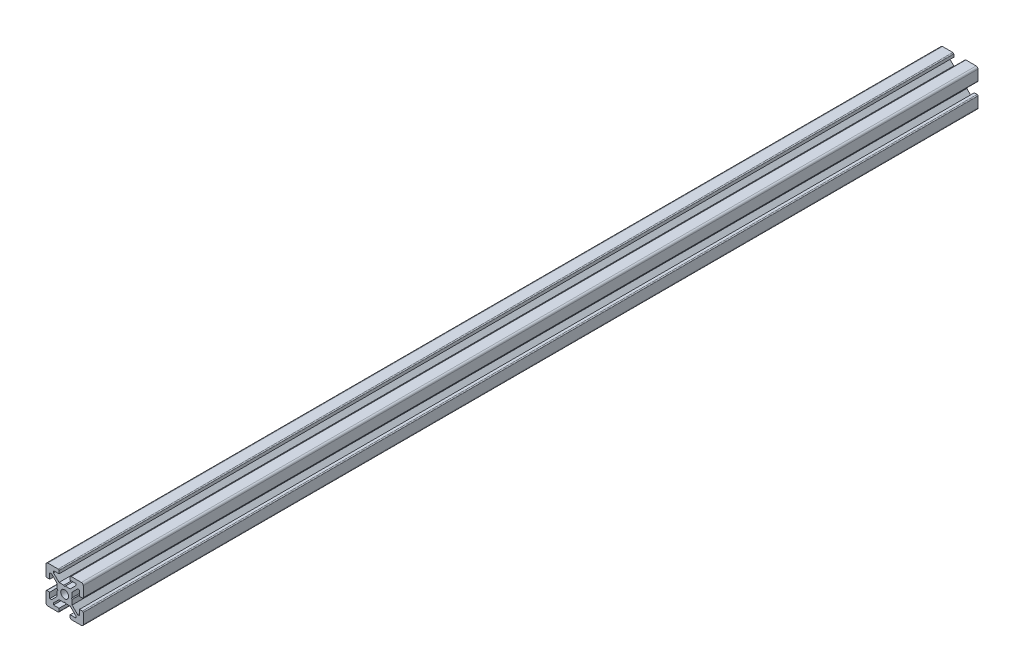
SolidWorks part; units mm, degrees
material "Lega 6061"
ref_plane "Piano frontale" through (0, 0, 0) normal (0, 0, 1) x (1, 0, 0)
ref_plane "Piano superiore" through (0, 0, 0) normal (0, 1, 0) x (1, 0, 0)
ref_plane "Piano destro" through (0, 0, 0) normal (1, 0, 0) x (0, 0, -1)
sketch "Schizzo1" plane through (0, 0, 0) normal (0, 0, 1) x (1, 0, 0)
  line L0 (0, 0) -> (-10, 0) construction
  line L1 (0, 0) -> (0, 10) construction
  line L2 (-3.6, 0) -> (-4, 0.4)
  line L3 (-4, 0.4) -> (-4, 3)
  line L4 (-4, 3) -> (-7, 6)
  line L5 (-7, 6) -> (-8, 6)
  line L6 (-8, 6) -> (-8, 3)
  line L7 (-8, 3) -> (-9.5, 3)
  line L8 (-10, 3.5) -> (-10, 9)
  line L9 (0, 0) -> (-10, 10) construction
  line L10 (0, 3.6) -> (-0.4, 4)
  line L11 (-0.4, 4) -> (-3, 4)
  line L12 (-3, 4) -> (-6, 7)
  line L13 (-6, 7) -> (-6, 8)
  line L14 (-6, 8) -> (-3, 8)
  line L15 (-3, 8) -> (-3, 9.5)
  line L16 (-3.5, 10) -> (-9, 10)
  line L17 (0, 0) -> (-10, -10) construction
  line L18 (-3.5, -10) -> (-9, -10)
  line L19 (-3, -8) -> (-3, -9.5)
  line L20 (-6, -8) -> (-3, -8)
  line L21 (-6, -7) -> (-6, -8)
  line L22 (-3, -4) -> (-6, -7)
  line L23 (-0.4, -4) -> (-3, -4)
  line L24 (0, -3.6) -> (-0.4, -4)
  line L25 (-10, -3.5) -> (-10, -9)
  line L26 (-8, -3) -> (-9.5, -3)
  line L27 (-8, -6) -> (-8, -3)
  line L28 (-7, -6) -> (-8, -6)
  line L29 (-4, -3) -> (-7, -6)
  line L30 (-4, -0.4) -> (-4, -3)
  line L31 (-3.6, 0) -> (-4, -0.4)
  line L32 (0, 0) -> (10, -10) construction
  line L33 (0, 0) -> (10, 10) construction
  line L34 (3.6, 0) -> (4, -0.4)
  line L35 (4, -0.4) -> (4, -3)
  line L36 (4, -3) -> (7, -6)
  line L37 (7, -6) -> (8, -6)
  line L38 (8, -6) -> (8, -3)
  line L39 (8, -3) -> (9.5, -3)
  line L40 (10, -3.5) -> (10, -9)
  line L41 (0, -3.6) -> (0.4, -4)
  line L42 (0.4, -4) -> (3, -4)
  line L43 (3, -4) -> (6, -7)
  line L44 (6, -7) -> (6, -8)
  line L45 (6, -8) -> (3, -8)
  line L46 (3, -8) -> (3, -9.5)
  line L47 (3.5, -10) -> (9, -10)
  line L48 (3.5, 10) -> (9, 10)
  line L49 (3, 8) -> (3, 9.5)
  line L50 (6, 8) -> (3, 8)
  line L51 (6, 7) -> (6, 8)
  line L52 (3, 4) -> (6, 7)
  line L53 (0.4, 4) -> (3, 4)
  line L54 (0, 3.6) -> (0.4, 4)
  line L55 (10, 3.5) -> (10, 9)
  line L56 (8, 3) -> (9.5, 3)
  line L57 (8, 6) -> (8, 3)
  line L58 (7, 6) -> (8, 6)
  line L59 (4, 3) -> (7, 6)
  line L60 (4, 0.4) -> (4, 3)
  line L61 (3.6, 0) -> (4, 0.4)
  arc A0 (-10, 9) -> (-9, 10) centre (-9, 9) cw
  arc A1 (-3, 9.5) -> (-3.5, 10) centre (-3.5, 9.5) ccw
  arc A2 (-9.5, 3) -> (-10, 3.5) centre (-9.5, 3.5) cw
  arc A3 (-9.5, -3) -> (-10, -3.5) centre (-9.5, -3.5) ccw
  arc A4 (-3, -9.5) -> (-3.5, -10) centre (-3.5, -9.5) cw
  arc A5 (-10, -9) -> (-9, -10) centre (-9, -9) ccw
  arc A6 (10, -9) -> (9, -10) centre (9, -9) cw
  arc A7 (3, -9.5) -> (3.5, -10) centre (3.5, -9.5) ccw
  arc A8 (9.5, -3) -> (10, -3.5) centre (9.5, -3.5) cw
  arc A9 (9.5, 3) -> (10, 3.5) centre (9.5, 3.5) ccw
  arc A10 (3, 9.5) -> (3.5, 10) centre (3.5, 9.5) cw
  arc A11 (10, 9) -> (9, 10) centre (9, 9) ccw
  circle A12 centre (0, 0) radius 2.1
  point P24 (-3, 10)
  point P27 (-10, 3)
  point P49 (-10, -3)
  point P50 (-3, -10)
  point P92 (3, -10)
  point P93 (10, -3)
  point P94 (10, 3)
  point P95 (3, 10)
  dimension "D2" = 1
  dimension "D12" = 0.5
  dimension "D13" = 4.2
  dimension "D3" = 8
  dimension "D4" = 0.4
  dimension "D5" = 45
  dimension "D6" = 6
  dimension "D7" = 12
  dimension "D8" = 20
  dimension "D9" = 2
  dimension "D10" = 4
  dimension "D11" = 45
extrude "Estrusione-Estrusione1" add sketch "Schizzo1" along normal blind 480
